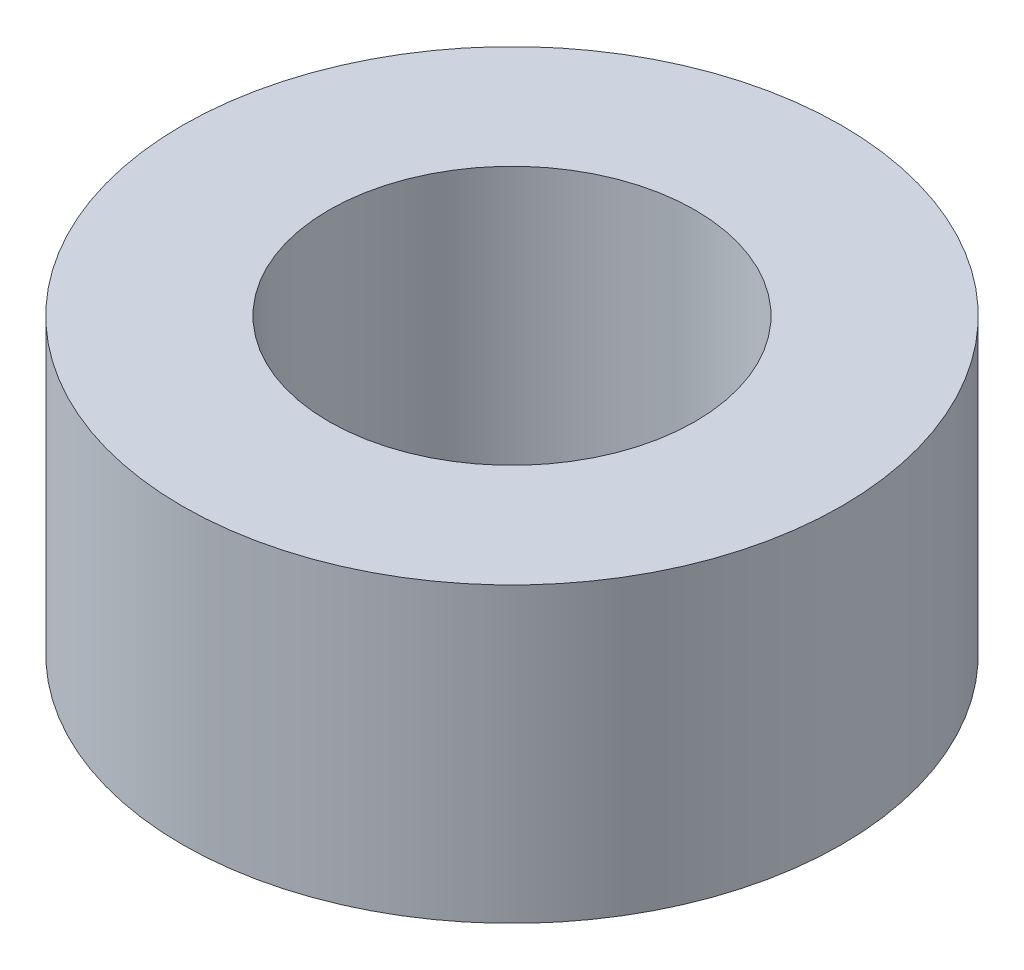
SolidWorks part; units mm, degrees
material "Nylon 101"
ref_plane "Front Plane" through (0, 0, 0) normal (0, 0, 1) x (1, 0, 0)
ref_plane "Top Plane" through (0, 0, 0) normal (0, 1, 0) x (1, 0, 0)
ref_plane "Right Plane" through (0, 0, 0) normal (1, 0, 0) x (0, 0, -1)
sketch "Sketch1" plane through (0, 0, 0) normal (0, 1, 0) x (1, 0, 0)
  circle A0 centre (0, 0) radius 7.1438
  circle A1 centre (0, 0) radius 3.9688
  dimension "D1" = 7.9375
  dimension "D2" = 3.175
extrude "Boss-Extrude1" add sketch "Sketch1" along normal blind 6.35
